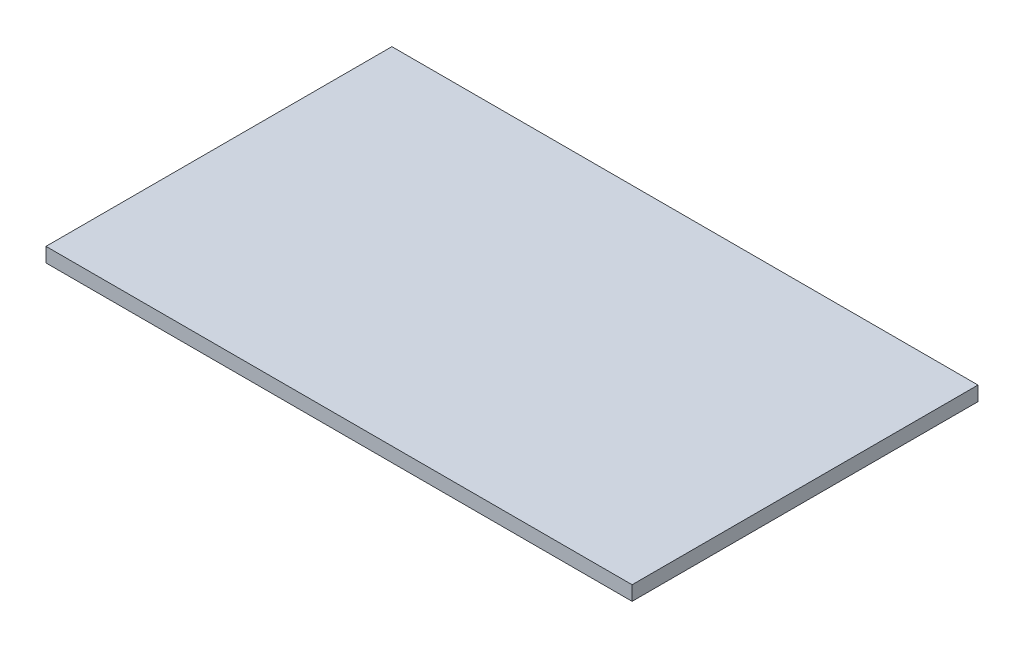
SolidWorks part; units mm, degrees
ref_plane "Front Plane" through (0, 0, 0) normal (0, 0, 1) x (1, 0, 0)
ref_plane "Top Plane" through (0, 0, 0) normal (0, 1, 0) x (1, 0, 0)
ref_plane "Right Plane" through (0, 0, 0) normal (1, 0, 0) x (0, 0, -1)
sketch "Sketch1" plane through (0, 0, 0) normal (0, 1, 0) x (1, 0, 0)
  line L1 (-46.2661, 27.642) -> (563.7339, 27.642)
  line L2 (-46.2661, 27.642) -> (-46.2661, -332.358)
  line L3 (-46.2661, -332.358) -> (563.7339, -332.358)
  line L4 (563.7339, 27.642) -> (563.7339, -332.358)
  dimension "D1" = 610
  dimension "D2" = 360
extrude "Boss-Extrude1" add sketch "Sketch1" along normal blind 15
